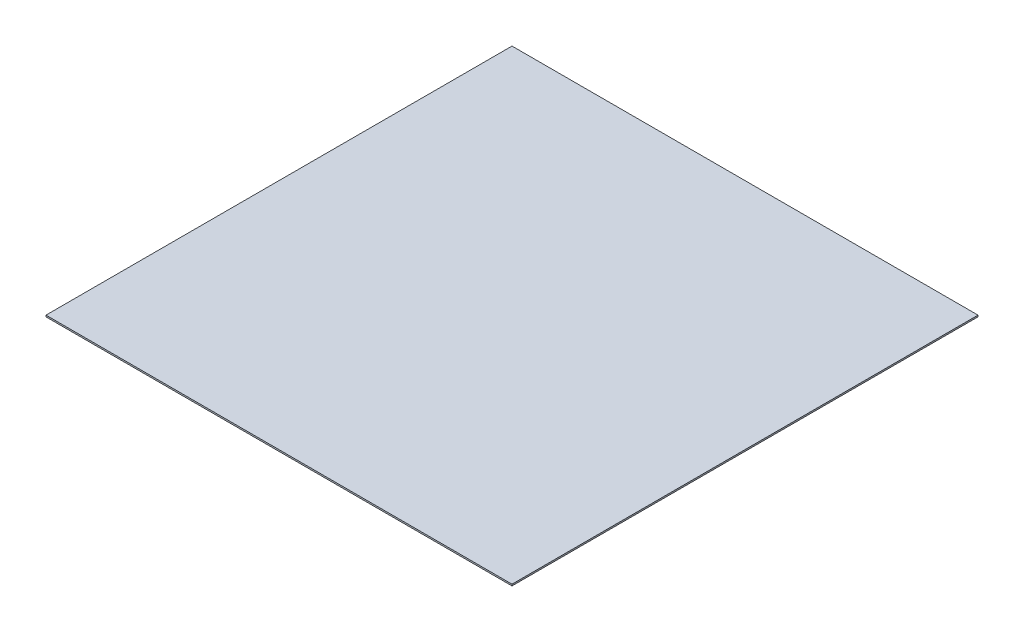
SolidWorks part; units mm, degrees
ref_plane "Front Plane" through (0, 0, 0) normal (0, 0, 1) x (1, 0, 0)
ref_plane "Top Plane" through (0, 0, 0) normal (0, 1, 0) x (1, 0, 0)
ref_plane "Right Plane" through (0, 0, 0) normal (1, 0, 0) x (0, 0, -1)
sketch "Sketch1" plane through (0, 0, 0) normal (0, 1, 0) x (1, 0, 0)
  line L1 (-1500, -1500) -> (1500, -1500)
  line L2 (-1500, -1500) -> (-1500, 1500)
  line L3 (-1500, 1500) -> (1500, 1500)
  line L4 (1500, -1500) -> (1500, 1500)
  line L5 (-1500, -1500) -> (1500, 1500) construction
  line L6 (-1500, 1500) -> (1500, -1500) construction
  point P0 (0, 0)
  dimension "D1" = 3000
  dimension "D2" = 3000
extrude "Boss-Extrude1" add sketch "Sketch1" along normal blind 10
